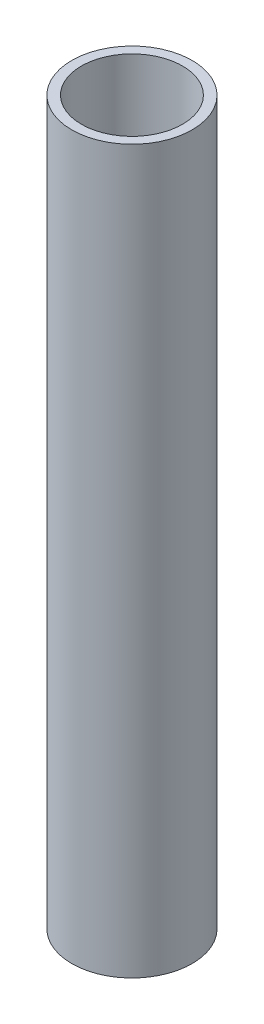
SolidWorks part; units mm, degrees
material "6061 Alloy"
ref_plane "Front Plane" through (0, 0, 0) normal (0, 0, 1) x (1, 0, 0)
ref_plane "Top Plane" through (0, 0, 0) normal (0, 1, 0) x (1, 0, 0)
ref_plane "Right Plane" through (0, 0, 0) normal (1, 0, 0) x (0, 0, -1)
sketch "Sketch1" plane through (0, 0, 0) normal (0, 1, 0) x (1, 0, 0)
  circle A0 centre (0, 0) radius 3.175
  dimension "D1" = 6.35
extrude "Boss-Extrude1" add sketch "Sketch1" along normal mid plane 38.1
sketch "Sketch2" plane through (0, 0, 0) normal (0, 1, 0) x (1, 0, 0)
  circle A0 centre (0, 0) radius 2.667
  dimension "D1" = 5.334
extrude "Cut-Extrude1" cut sketch "Sketch2" against normal through all and the other way through all
